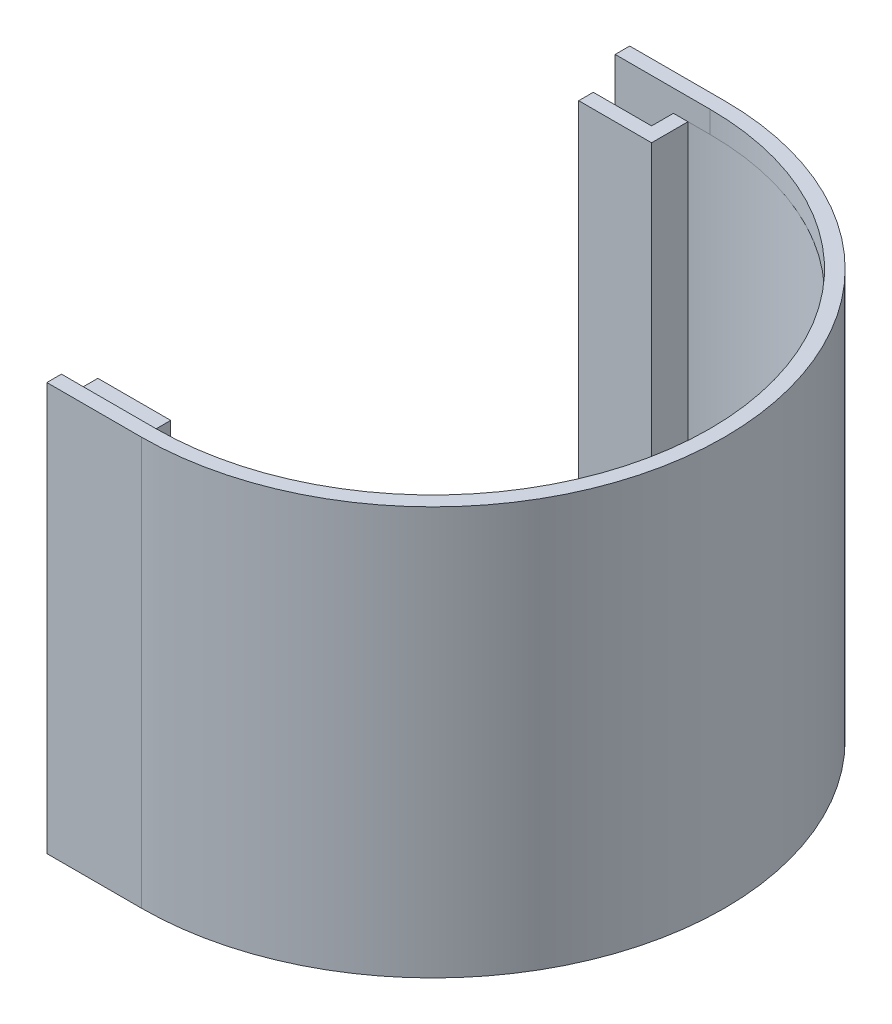
SolidWorks part; units mm, degrees
material "Mahogany"
ref_plane "Front Plane" through (0, 0, 0) normal (0, 0, 1) x (1, 0, 0)
ref_plane "Top Plane" through (0, 0, 0) normal (0, 1, 0) x (1, 0, 0)
ref_plane "Right Plane" through (0, 0, 0) normal (1, 0, 0) x (0, 0, -1)
sketch "Sketch6" plane through (0, 0, 0) normal (0, 1, 0) x (1, 0, 0)
  line L2 (0, 40) -> (-13, 40)
  line L3 (-13, 40) -> (-13, 38)
  line L4 (-55, 0) -> (55, 0) construction
  line L5 (-13, 38) -> (-5, 38)
  line L6 (-5, 38) -> (-5, 35)
  line L7 (-5, 35) -> (-13, 35)
  line L8 (-13, 35) -> (-13, 33)
  line L9 (-13, 33) -> (-3, 33)
  line L10 (-3, 33) -> (-3, 38)
  line L11 (-3, -33) -> (-3, -38)
  line L12 (-13, -33) -> (-3, -33)
  line L13 (-13, -35) -> (-13, -33)
  line L14 (-5, -35) -> (-13, -35)
  line L15 (-5, -38) -> (-5, -35)
  line L16 (-13, -38) -> (-5, -38)
  line L17 (-13, -40) -> (-13, -38)
  line L18 (0, -40) -> (-13, -40)
  arc A0 (0, 40) -> (0, -40) centre (0, 0) cw
  arc A1 (-3, 38) -> (-3, -38) centre (0, 0) cw
  dimension "D2" = 40
  dimension "D3" = 2
  dimension "D4" = 2
  dimension "D5" = 3
  dimension "D6" = 13
  dimension "D7" = 10
  dimension "D8" = 5
  dimension "D9" = 2
extrude "Boss-Extrude1" add sketch "Sketch6" along normal blind 50
sketch "Sketch7" plane through (0, 50, 0) normal (0, 1, 0) x (1, 0, 0)
  line L0 (-13, -40) -> (0, -40) construction
  line L3 (0, -38) -> (-13, -38)
  line L4 (-13, -38) -> (-13, -40)
  line L5 (-13, -40) -> (0, -40)
  line L6 (0, 40) -> (-13, 40)
  line L7 (-13, 40) -> (-13, 38)
  line L8 (-13, 38) -> (0, 38)
  line L9 (-5, -38) -> (-13, -38) construction
  arc A0 (0, 40) -> (0, -40) centre (0, 0) cw
  arc A1 (0, 38) -> (0, -38) centre (0, 0) cw
  dimension "D1" = 2
extrude "Boss-Extrude2" add sketch "Sketch7" along normal blind 3
sketch "Sketch8" plane through (0, 0, 0) normal (0, -1, 0) x (1, 0, 0)
  line L2 (0, -40) -> (-13, -40)
  line L3 (0, -40) -> (-13, -40) construction
  line L4 (-13, -40) -> (-13, -38)
  line L5 (-13, -38) -> (0, -38)
  line L6 (0, 38) -> (-13, 38)
  line L7 (-13, 38) -> (-13, 40)
  line L8 (-13, 40) -> (0, 40)
  arc A0 (0, 40) -> (0, -40) centre (0, 0) cw
  arc A1 (0, -40) -> (0, 40) centre (0, 0) ccw construction
  arc A2 (0, 38) -> (0, -38) centre (0, 0) cw
  dimension "D1" = 2
extrude "Boss-Extrude3" add sketch "Sketch8" along normal blind 3
